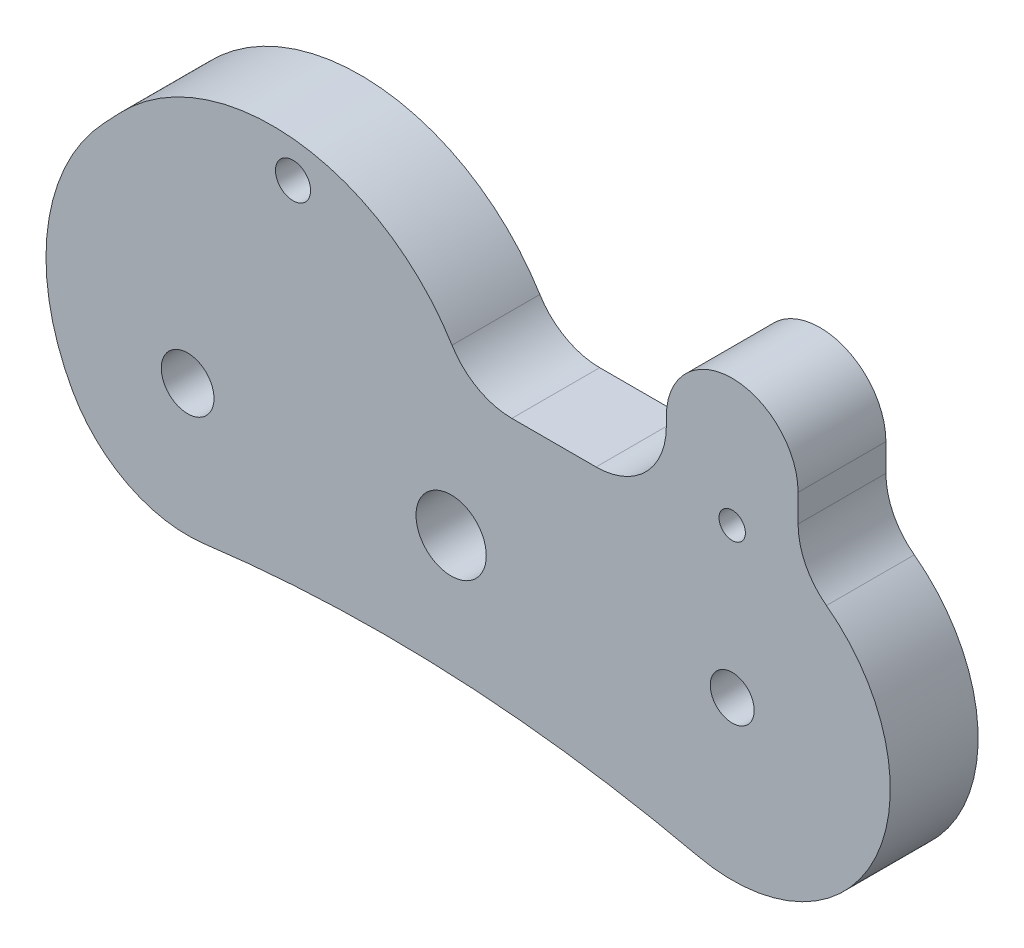
SolidWorks part; units mm, degrees
material "PMMA"
ref_plane "Front Plane" through (0, 0, 0) normal (0, 0, 1) x (1, 0, 0)
ref_plane "Top Plane" through (0, 0, 0) normal (0, 1, 0) x (1, 0, 0)
ref_plane "Right Plane" through (0, 0, 0) normal (1, 0, 0) x (0, 0, -1)
sketch "Sketch1" plane through (0, 0, 0) normal (0, 0, 1) x (1, 0, 0)
  line L0 (0, 0) -> (31, 0) construction
  line L1 (18.4575, 7.5) -> (23.25, 7.5)
  line L2 (27.25, 12) -> (27.25, 11.5)
  line L3 (34.75, 12) -> (34.75, 10.4373)
  line L4 (-3.8797, 11.3747) -> (-4.7707, 10.4349)
  circle A0 centre (0, 0) radius 1.5
  circle A1 centre (31, 0) radius 1.25
  circle A2 centre (15, 0) radius 2
  circle A3 centre (6, 13) radius 1
  circle A4 centre (31, 8.5) radius 0.75
  arc A5 (29.0008, -8.7751) -> (36.3654, 7.2258) centre (31, 0) ccw
  arc A7 (-6.5625, -3.6309) -> (0.9626, -7.438) centre (0, 0) ccw
  arc A8 (0.9626, -7.438) -> (29.0008, -8.7751) centre (11.2298, -86.7764) cw
  arc A10 (-6.5625, -3.6309) -> (-4.7707, 10.4349) centre (3.9375, 2.1786) cw
  arc A11 (27.25, 11.5) -> (23.25, 7.5) centre (23.25, 11.5) cw
  arc A13 (34.75, 12) -> (27.25, 12) centre (31, 12) ccw
  arc A14 (-3.8797, 11.3747) -> (15.0503, 9.4046) centre (4.8285, 3.1184) cw
  arc A15 (18.4575, 7.5) -> (15.0503, 9.4046) centre (18.4575, 11.5) cw
  arc A16 (36.3654, 7.2258) -> (34.75, 10.4373) centre (38.75, 10.4373) cw
  point P30 (16, 7.5)
  dimension "D2" = 3
  dimension "D3" = 2.5
  dimension "D5" = 4
  dimension "D6" = 2
  dimension "D9" = 1.5
  dimension "D12" = 18
  dimension "D13" = 12
  dimension "D15" = 15
  dimension "D16" = 80
  dimension "D17" = 4
  dimension "D19" = 12
  dimension "D21" = 6.5625
  dimension "D23" = 11.3747
  dimension "D18" = 4
  dimension "D24" = 23.25
  dimension "D25" = 3.75
  dimension "D1" = 31
  dimension "D4" = 15
  dimension "D7" = 6
  dimension "D8" = 13
  dimension "D10" = 8.5
  dimension "D11" = 31
  dimension "D14" = 12
  dimension "D20" = 7.5
  dimension "D22" = 16
extrude "Boss-Extrude1" add sketch "Sketch1" along normal blind 5
cosmetic thread "Cosmetic Thread1" parameters "D2"=2
cosmetic thread "Cosmetic Thread2" parameters "D2"=3
